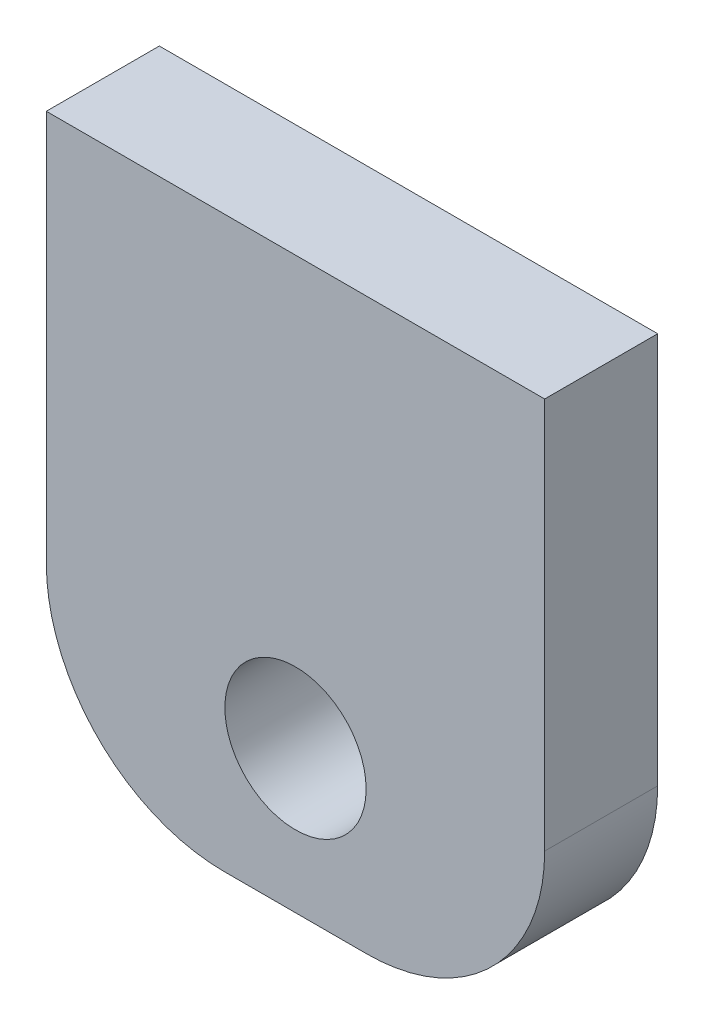
SolidWorks part; units mm, degrees
ref_plane "Alzado" through (0, 0, 0) normal (0, 0, 1) x (1, 0, 0)
ref_plane "Planta" through (0, 0, 0) normal (0, 1, 0) x (1, 0, 0)
ref_plane "Vista lateral" through (0, 0, 0) normal (1, 0, 0) x (0, 0, -1)
sketch "Croquis1" plane through (0, 0, 0) normal (0, 0, 1) x (1, 0, 0)
  line L0 (14, -32) -> (14, -24) construction
  line L1 (0, 0) -> (28, 0)
  line L2 (0, 0) -> (0, -32)
  line L3 (0, -32) -> (28, -32)
  line L4 (28, 0) -> (28, -32)
  circle A0 centre (14, -24) radius 3.9688
  dimension "D3" = 7.9375
  dimension "D1" = 28
  dimension "D2" = 32
  dimension "D4" = 8
extrude "Saliente-Extruir1" add sketch "Croquis1" along normal blind 6.35
fillet "Redondeo1" radius 10 2 edges at (0, -32, 3.175) (28, -32, 3.175)
